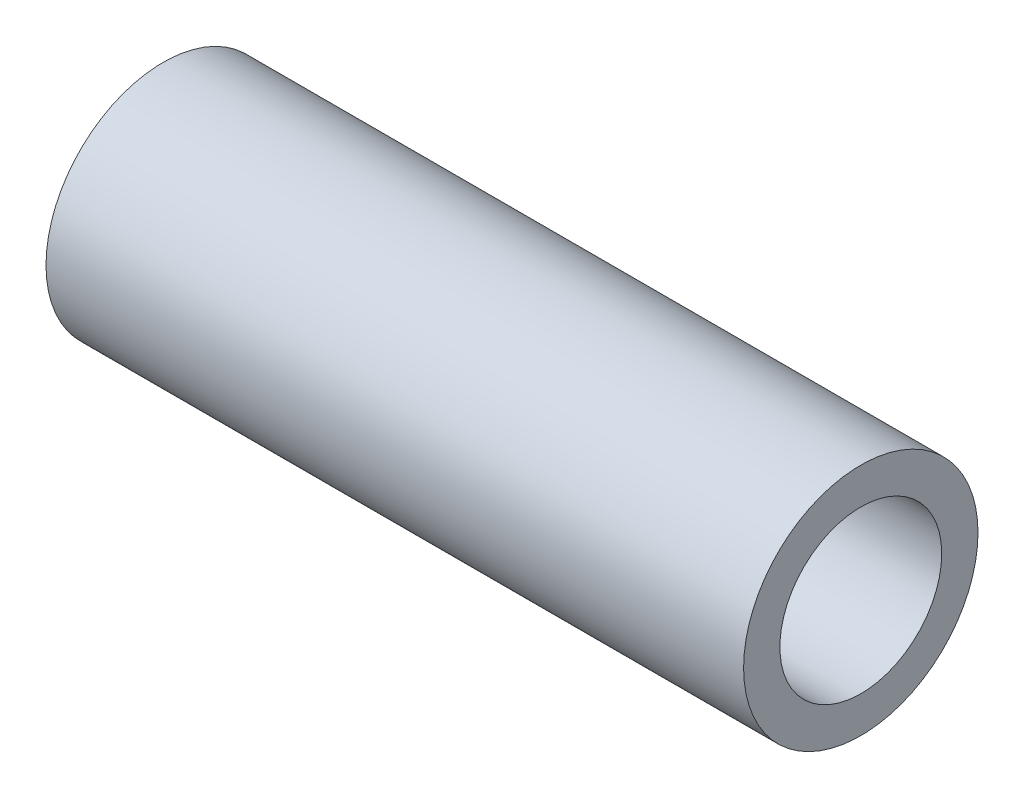
SolidWorks part; units mm, degrees
material "PVC 0.007 Plasticized"
ref_plane "Front Plane" through (0, 0, 0) normal (0, 0, 1) x (1, 0, 0)
ref_plane "Top Plane" through (0, 0, 0) normal (0, 1, 0) x (1, 0, 0)
ref_plane "Right Plane" through (0, 0, 0) normal (1, 0, 0) x (0, 0, -1)
sketch "Sketch1" plane through (0, 0, 0) normal (1, 0, 0) x (0, 0, -1)
  circle A0 centre (0, 0) radius 10.668
  circle A1 centre (0, 0) radius 7.366
  dimension "D1" = 21.336
  dimension "D2" = 14.732
extrude "Boss-Extrude1" add sketch "Sketch1" against normal blind 63.5
